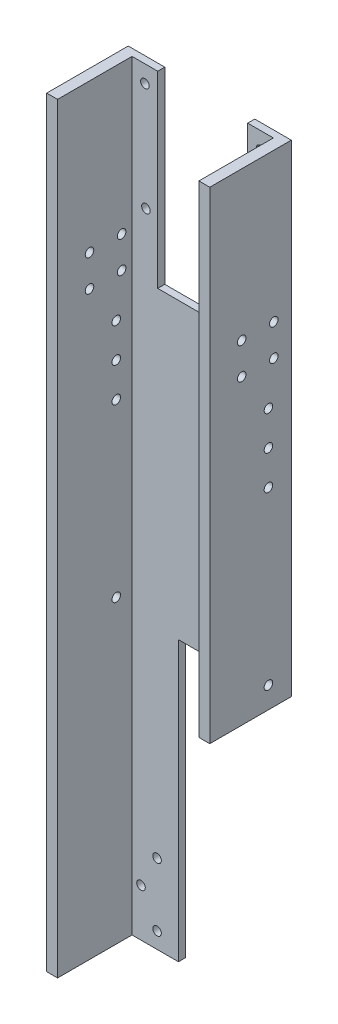
SolidWorks part; units mm, degrees
ref_plane "Front" through (0, 0, 0) normal (0, 0, 1) x (1, 0, 0)
ref_plane "Top" through (0, 0, 0) normal (0, 1, 0) x (1, 0, 0)
ref_plane "Right" through (0, 0, 0) normal (1, 0, 0) x (0, 0, -1)
sketch "Sketch1" plane through (0, 0, 0) normal (0, 1, 0) x (1, 0, 0)
  line L0 (-38.1, -19.05) -> (-33.02, -19.05)
  line L1 (-38.1, -19.05) -> (38.1, -19.05) construction
  line L2 (-38.1, -19.05) -> (-38.1, 19.05)
  line L3 (-38.1, 19.05) -> (38.1, 19.05)
  line L4 (38.1, -19.05) -> (38.1, 19.05)
  line L5 (-38.1, -19.05) -> (38.1, 19.05) construction
  line L6 (-38.1, 19.05) -> (38.1, -19.05) construction
  line L7 (-33.02, -19.05) -> (-33.02, 15.748)
  line L8 (-33.02, 15.748) -> (33.02, 15.748)
  line L9 (33.02, 15.748) -> (33.02, -19.05)
  line L10 (33.02, -19.05) -> (38.1, -19.05)
  point P0 (0, 0)
  dimension "D1" = 76.2
  dimension "D2" = 38.1
  dimension "D3" = 3.302
  dimension "D4" = 5.08
extrude "Boss-Extrude1" add sketch "Sketch1" along normal mid plane 355.6
sketch "Sketch2" plane through (0, 0, -15.748) normal (0, 0, 1) x (1, 0, 0)
  line L0 (-33.02, 177.8) -> (-33.02, -177.8) construction
  line L1 (-33.02, 177.8) -> (-27.0204, 177.8) construction
  line L2 (-33.02, 177.8) -> (-33.02, 169.8) construction
  line L3 (-33.02, 169.8) -> (-27.0204, 169.8) construction
  line L4 (-27.0204, 177.8) -> (-27.0204, 169.8) construction
  line L5 (-21.0207, 177.8) -> (-21.0207, 89.8924)
  line L6 (-33.02, 177.8) -> (33.02, 177.8) construction
  line L8 (-33.02, 177.8) -> (-21.0207, 177.8) construction
  line L9 (-21.0207, 89.8924) -> (0, 89.8924)
  line L10 (-21.0207, 177.8) -> (0, 177.8)
  line L11 (0, 177.8) -> (0, 89.8924)
  circle A0 centre (-27.0204, 169.8) radius 2
  circle A1 centre (-26.52, 119.4757) radius 2
  circle A2 centre (-13.52, 125.8257) radius 1.5 construction
  arc A3 (-13.52, 125.8257) -> (-14.5207, 111.3924) centre (-26.52, 119.4757) cw construction
  arc A4 (-13.2767, 110.5543) -> (-12.1722, 126.484) centre (-26.52, 119.4757) ccw construction
  arc A5 (-15.7648, 112.2304) -> (-14.8678, 125.1673) centre (-26.52, 119.4757) ccw construction
  arc A6 (-15.7648, 112.2304) -> (-13.2767, 110.5543) centre (-14.5207, 111.3924) ccw construction
  arc A7 (-12.1722, 126.484) -> (-14.8678, 125.1673) centre (-13.52, 125.8257) ccw construction
  point P10 (-12.0867, 118.475)
  dimension "D2" = 4
  dimension "D7" = 4
  dimension "D8" = 3
  dimension "D10" = 5
  dimension "D12" = 20
  dimension "D1" = 8
  dimension "D3" = 13
  dimension "D4" = 6.35
  dimension "D5" = 6.5
  dimension "D6" = 46
  dimension "D9" = 60
  dimension "D11" = 5.4993
extrude "Cut-Extrude1" cut sketch "Sketch2" against normal through all
mirror "Mirror1" about plane through (0, 0, 0) normal (1, 0, 0) of "Cut-Extrude1"
sketch "Sketch4" plane through (0, 0, -15.748) normal (0, 0, 1) x (1, 0, 0)
  line L0 (-16.335, -177.8) -> (-16.335, -133.35) construction
  line L1 (-33.02, -177.8) -> (33.02, -177.8) construction
  line L2 (-38.1, 177.8) -> (-38.1, -177.8) construction
  circle A0 centre (-21.335, -170.3) radius 2
  circle A1 centre (-28.835, -155.575) radius 2
  circle A2 centre (-21.335, -140.85) radius 2
  dimension "D8" = 4
  dimension "D1" = 21.765
  dimension "D2" = 44.45
  dimension "D3" = 5
  dimension "D4" = 7.5
  dimension "D5" = 14.725
  dimension "D6" = 29.45
  dimension "D7" = 7.5
extrude "Cut-Extrude2" cut sketch "Sketch4" against normal through all
sketch "Sketch5" plane through (-38.1, 0, 0) normal (-1, 0, 0) x (0, 0, 1)
  line L0 (-19.05, 177.8) -> (19.05, 177.8) construction
  line L1 (-19.05, 177.8) -> (-19.05, -177.8) construction
  line L2 (-8.375, 74.5851) -> (-8.375, 42.5851) construction
  line L3 (19.05, 86.138) -> (-15.875, 86.138) construction
  line L4 (19.05, 177.8) -> (19.05, -177.8) construction
  line L5 (-10.875, 93.638) -> (4.125, 93.638) construction
  line L6 (-10.875, 93.638) -> (-10.875, 108.363) construction
  circle A0 centre (-8.375, 58.5851) radius 2
  circle A1 centre (-8.375, 74.5851) radius 2
  circle A2 centre (-8.375, 42.5851) radius 2
  circle A3 centre (-8.375, -37.4269) radius 2
  circle A4 centre (-10.875, 93.638) radius 2
  circle A5 centre (4.125, 93.638) radius 2
  circle A6 centre (4.125, 108.363) radius 2
  circle A7 centre (-10.875, 108.363) radius 2
  dimension "D3" = 4
  dimension "D1" = 119.2149
  dimension "D2" = 10.675
  dimension "D4" = 16
  dimension "D5" = 215.2269
  dimension "D6" = 91.662
  dimension "D7" = 34.925
  dimension "D8" = 7.5
  dimension "D9" = 5
  dimension "D12" = 90
  dimension "D13" = 15
  dimension "D14" = 14.725
  dimension "D10" = 2
  dimension "D11" = 2
extrude "Cut-Extrude3" cut sketch "Sketch5" against normal through all
sketch "Sketch6" plane through (0, 0, 19.05) normal (0, 0, 1) x (1, 0, 0)
  line L0 (38.1, -47.4269) -> (-11.335, -47.4269)
  line L1 (38.1, 177.8) -> (38.1, -177.8) construction
  line L3 (-11.335, -47.4269) -> (-11.335, -177.8)
  line L4 (-33.02, -177.8) -> (33.02, -177.8) construction
  circle A0 centre (-21.335, -140.85) radius 2 construction
  dimension "D2" = 10
  dimension "D1" = 10
extrude "Cut-Extrude4" cut sketch "Sketch6" against normal through all and the other way through all
